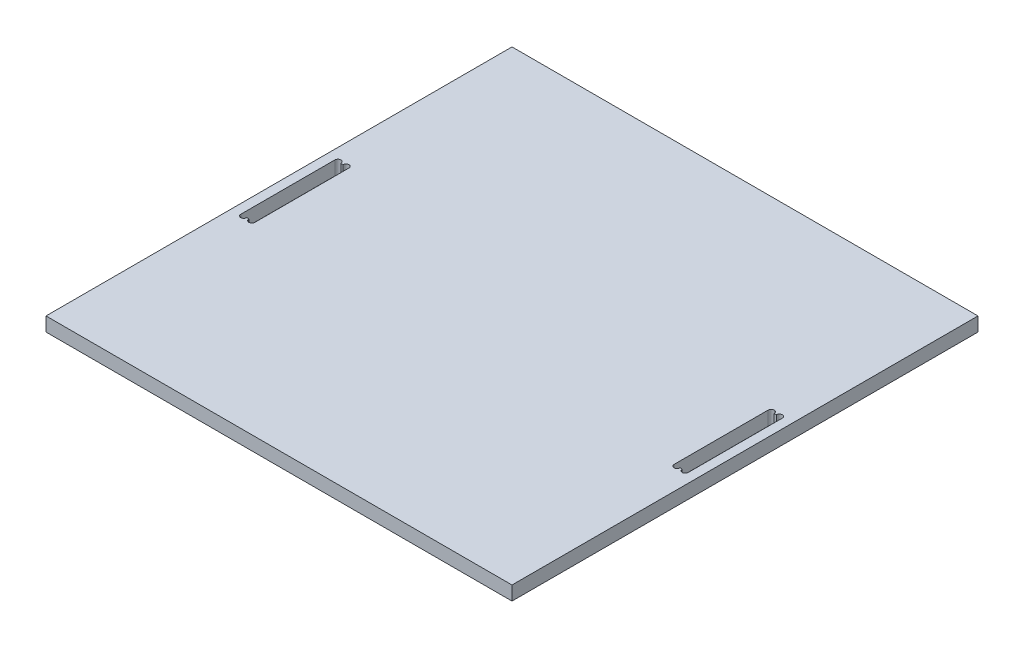
SolidWorks part; units mm, degrees
ref_plane "Alzado" through (0, 0, 0) normal (0, 0, 1) x (1, 0, 0)
ref_plane "Planta" through (0, 0, 0) normal (0, 1, 0) x (1, 0, 0)
ref_plane "Vista lateral" through (0, 0, 0) normal (1, 0, 0) x (0, 0, -1)
sketch "Croquis1" plane through (0, 0, 0) normal (0, 1, 0) x (1, 0, 0)
  line L0 (0, 282.1544) -> (0, -291.5263) construction
  line L1 (-250, 250) -> (250, 250)
  line L2 (-250, 250) -> (-250, -250)
  line L3 (-250, -250) -> (250, -250)
  line L4 (250, 250) -> (250, -250)
  line L5 (-250, 250) -> (250, -250) construction
  line L6 (-250, -250) -> (250, 250) construction
  point P0 (0, 0)
  dimension "D1" = 500
  dimension "D2" = 500
extrude "Saliente-Extruir1" add sketch "Croquis1" along normal blind 15 contours L2 L3 L4 L1
sketch "Croquis3" plane through (0, 15, 0) normal (0, 1, 0) x (1, 0, 0)
  line L0 (-250, 250) -> (-250, -250) construction
  line L1 (-240, 50) -> (-224.9, 50)
  line L2 (-240, 50) -> (-240, -51)
  line L3 (-240, -51) -> (-224.9, -51)
  line L4 (-224.9, 50) -> (-224.9, -51)
  line L5 (-240, 50) -> (-224.9, -51) construction
  line L6 (-240, -51) -> (-224.9, 50) construction
  line L8 (0, -375.6406) -> (0, 378.4486) construction
  line L9 (240, -51) -> (224.9, -51)
  line L10 (240, 50) -> (240, -51)
  line L11 (240, 50) -> (224.9, 50)
  line L12 (224.9, 50) -> (224.9, -51)
  line L20 (-250, 250) -> (250, 250) construction
  dimension "D1" = 10
  dimension "D2" = 101
  dimension "D3" = 200
  dimension "D4" = 15.1
extrude "Cortar-Extruir1" cut sketch "Croquis3" against normal through all
sketch "Croquis4" plane through (0, 15, 0) normal (0, 1, 0) x (1, 0, 0)
  line L0 (-389.0787, 0) -> (451.4343, 0) construction
  line L1 (0, -363.0729) -> (0, 353.6329) construction
  line L2 (-224.9, -51) -> (-224.9, 50) construction
  line L4 (-240, -51) -> (-224.9, -51) construction
  line L5 (-240, 50) -> (-240, -51) construction
  line L10 (-224.9, 50) -> (-240, 50) construction
  line L11 (224.9, 50) -> (224.9, -51) construction
  line L12 (240, 50) -> (224.9, 50) construction
  line L13 (240, -51) -> (240, 50) construction
  circle A0 centre (-228.1, -51) radius 3.2
  circle A2 centre (-236.8, -51) radius 3.2
  circle A3 centre (-228.075, 50) radius 3.175
  circle A4 centre (-236.825, 50) radius 3.175
  circle A5 centre (236.8, -51) radius 3.2
  circle A6 centre (228.1, -51) radius 3.2
  circle A7 centre (228.075, 50) radius 3.175
  circle A8 centre (236.825, 50) radius 3.175
extrude "Cortar-Extruir2" cut sketch "Croquis4" against normal through all
equation "\"L\"= 60cm'Length"
equation "\"D\"= 60cm'Depth"
equation "\"T\"= 15'Thick"
equation "\"D1@Saliente-Extruir1\"=\"T\""
equation "\"R\"= 3.2'Tool´s radius"
equation "\"D1@Croquis4\"=\"R\""
equation "\"D2@Croquis4\"=\"R\""
